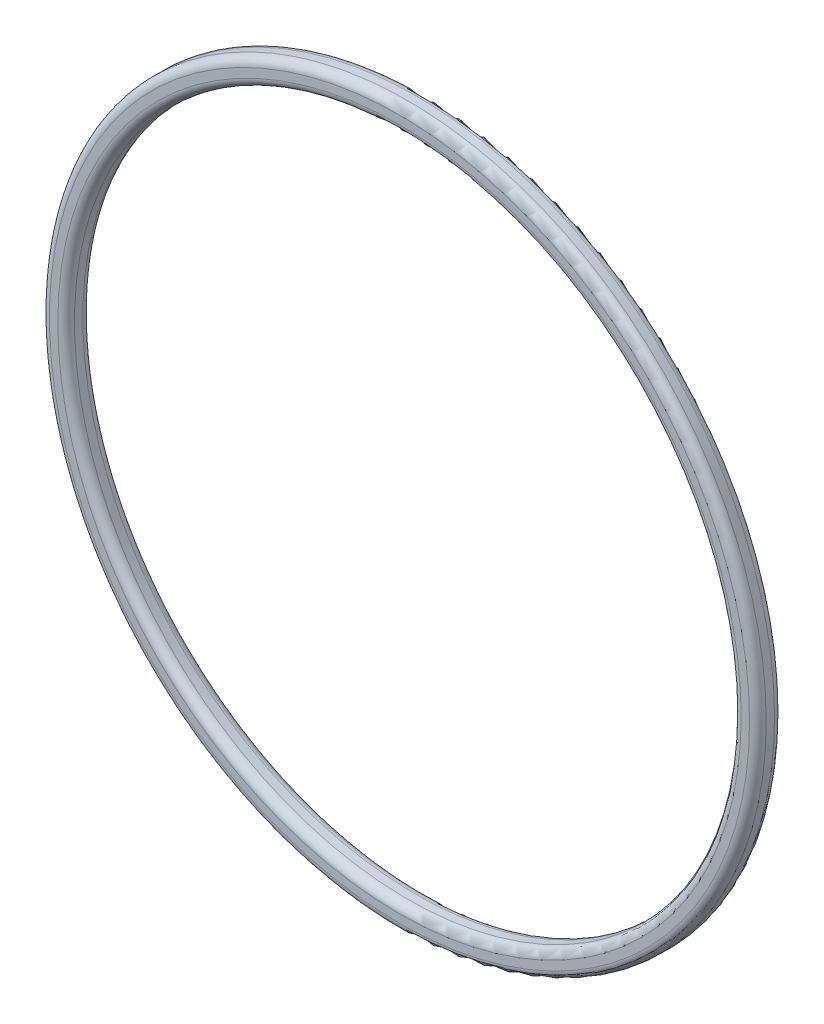
SolidWorks part; units mm, degrees
material "Gomma siliconata"
ref_plane "Piano frontale" through (0, 0, 0) normal (0, 0, 1) x (1, 0, 0)
ref_plane "Piano superiore" through (0, 0, 0) normal (0, 1, 0) x (1, 0, 0)
ref_plane "Piano destro" through (0, 0, 0) normal (1, 0, 0) x (0, 0, -1)
sketch "Schizzo1" plane through (0, 0, 0) normal (0, 0, 1) x (1, 0, 0)
  circle A0 centre (0, 0) radius 40
  circle A1 centre (0, 0) radius 43
  dimension "D1" = 80
  dimension "D2" = 86
extrude "Estrusione-Estrusione1" add sketch "Schizzo1" along normal blind 3
fillet "Raccordo1" radius 1 4 edges at (40, 0, 0) (43, 0, 0) (40, 0, 3) (43, 0, 3)
